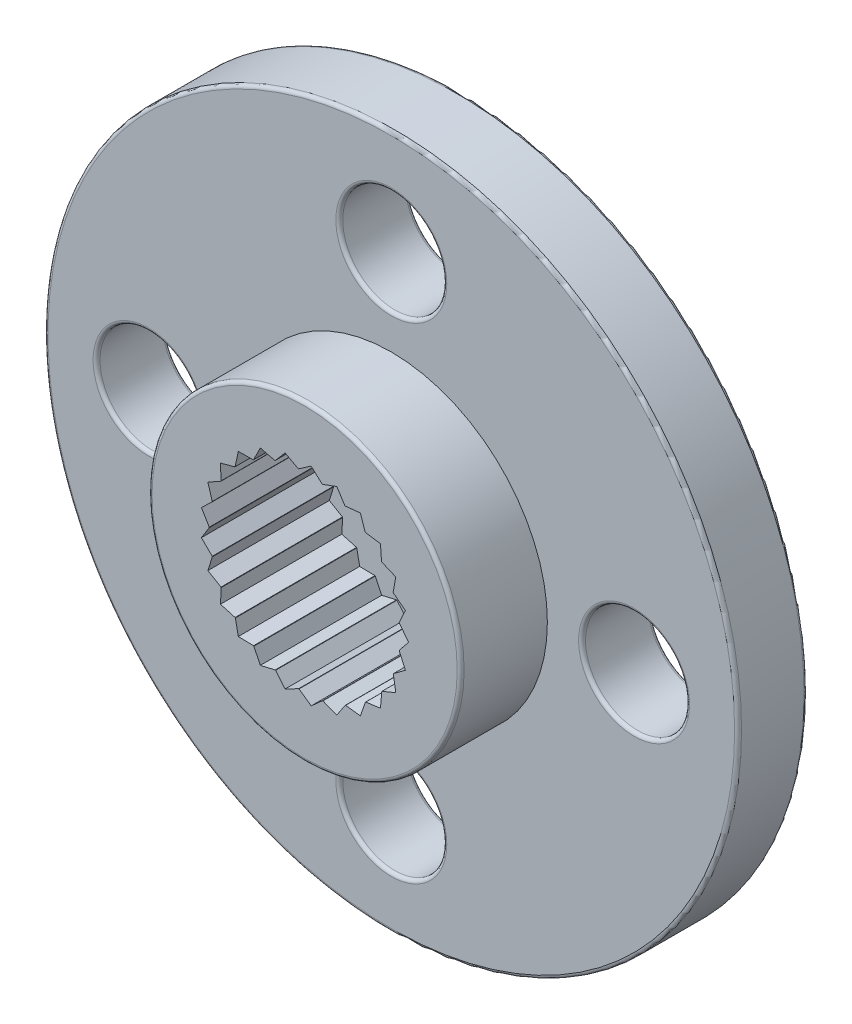
SolidWorks part; units mm, degrees
material "1060 Alloy"
ref_plane "Front Plane" through (0, 0, 0) normal (0, 0, 1) x (1, 0, 0)
ref_plane "Top Plane" through (0, 0, 0) normal (0, 1, 0) x (1, 0, 0)
ref_plane "Right Plane" through (0, 0, 0) normal (1, 0, 0) x (0, 0, -1)
sketch "Sketch1" plane through (0, 0, 0) normal (0, 0, 1) x (1, 0, 0)
  circle A0 centre (0, 0) radius 10
extrude "Boss-Extrude1" add sketch "Sketch1" along normal blind 2
sketch "Sketch2" plane through (0, 0, 2) normal (0, 0, 1) x (1, 0, 0)
  circle A0 centre (0, 0) radius 4.5
extrude "Boss-Extrude2" add sketch "Sketch2" along normal blind 2.5
sketch "Sketch3" plane through (0, 0, 4.5) normal (0, 0, 1) x (1, 0, 0)
  circle A0 centre (0, 0) radius 2.75
  dimension "D1" = 5.5
extrude "Cut-Extrude1" cut sketch "Sketch3" against normal blind 3.5
sketch "Sketch4" plane through (0, 0, 1) normal (0, 0, 1) x (1, 0, 0)
  circle A0 centre (0, 0) radius 1.5
extrude "Cut-Extrude2" cut sketch "Sketch4" against normal through all
sketch "Sketch5" plane through (0, 0, 4.5) normal (0, 0, 1) x (1, 0, 0)
  line L1 (-2.6565, 0.6821) -> (-2.6823, 0.6062)
  line L3 (-2.75, 0) -> (-2.9763, 0.376)
  line L4 (-2.9763, 0.376) -> (-2.6565, 0.6821)
  line L5 (-2.6823, 0.6062) -> (-2.75, 0)
  circle A2 centre (0, 0) radius 2.75 construction
extrude "Cut-Extrude3" cut sketch "Sketch5" against normal blind 3.5 contours L5 L3 L4 L1
pattern_circular "CirPattern1" count 25 over 360 about axis through (0, 0, 0) along (0, 0, 1) of "Cut-Extrude3"
sketch "Sketch6" plane through (0, 0, 2) normal (0, 0, 1) x (1, 0, 0)
  line L0 (0, 10) -> (0, -10) construction
  line L1 (0, -10) -> (10, 0) construction
  line L2 (10, 0) -> (-10, 0) construction
  line L3 (0, 0) -> (-7.0711, 7.0711) construction
  circle A0 centre (0, 0) radius 10 construction
  circle A1 centre (-7, 0) radius 1.5
  circle A2 centre (7, 0) radius 1.5
  circle A3 centre (0, 7) radius 1.5
  circle A4 centre (0, -7) radius 1.5
  dimension "D1" = 3
extrude "Cut-Extrude4" cut sketch "Sketch6" against normal through all
fillet "Fillet1" radius 0.1 1 edges at (5.5, 0, 2)
fillet "Fillet2" radius 0.1 12 edges at (10, 0, 0) (10, 0, 2) (1.5, 0, 0) (1.5, 0, 1) (4.5, 0, 4.5) (-1.5, 7, 0) (-1.5, 7, 2) (-5.5, 0, 0) (-5.5, 0, 2) (1.5, -7, 2) (1.5, -7, 0) (5.5, 0, 0)
